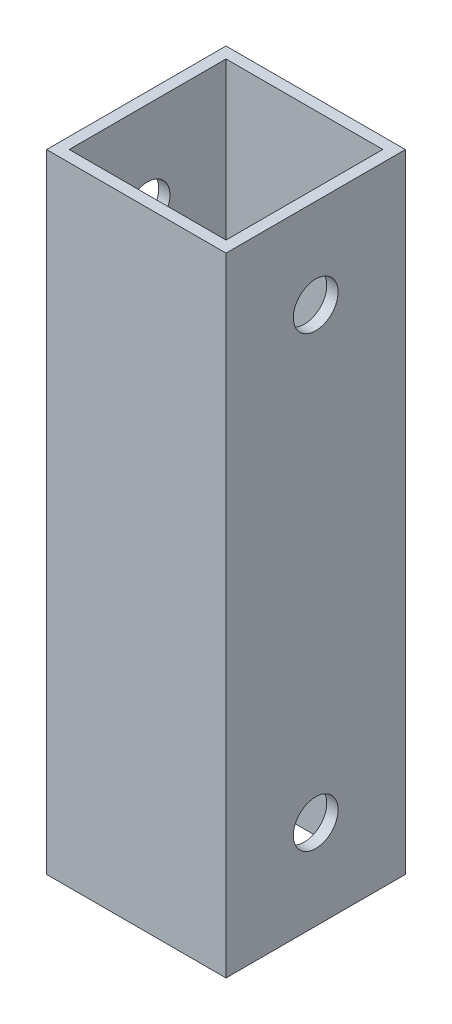
SolidWorks part; units mm, degrees
material "6061 Alloy"
ref_plane "Front Plane" through (0, 0, 0) normal (0, 0, 1) x (1, 0, 0)
ref_plane "Top Plane" through (0, 0, 0) normal (0, 1, 0) x (1, 0, 0)
ref_plane "Right Plane" through (0, 0, 0) normal (1, 0, 0) x (0, 0, -1)
sketch "Sketch1" plane through (0, 0, 0) normal (0, 1, 0) x (1, 0, 0)
  line L0 (-25.4, -25.4) -> (25.4, 25.4) construction
  line L1 (-25.4, 25.4) -> (25.4, 25.4)
  line L2 (-25.4, 25.4) -> (-25.4, -25.4)
  line L3 (-25.4, -25.4) -> (25.4, -25.4)
  line L4 (25.4, 25.4) -> (25.4, -25.4)
  line L5 (22.225, -22.225) -> (-22.225, 22.225) construction
  line L6 (-22.225, 22.225) -> (22.1918, 22.225)
  line L7 (-22.225, 22.225) -> (-22.225, -22.1918)
  line L8 (-22.225, -22.1918) -> (22.1918, -22.1918)
  line L9 (22.1918, 22.225) -> (22.1918, -22.1918)
  point P7 (0, 0)
  point P10 (0, 0)
  point P14 (0, 0)
  dimension "D1" = 50.8
  dimension "D2" = 3.175
  dimension "D3" = 3.175
extrude "Boss-Extrude1" add sketch "Sketch1" along normal blind 177.8
sketch "Sketch2" plane through (-25.4, 0, 0) normal (-1, 0, 0) x (0, 0, 1)
  line L0 (25.4, 88.9) -> (-25.4, 88.9) construction
  line L1 (25.4, 177.8) -> (25.4, 0) construction
  line L2 (-25.4, 177.8) -> (-25.4, 0) construction
  line L4 (0, 152.4) -> (0, 25.4) construction
  circle A1 centre (0, 25.4) radius 6.35
  circle A2 centre (0, 152.4) radius 6.35
  point P10 (0, 88.9)
  point P13 (0, 88.9)
  dimension "D2" = 12.7
extrude "Cut-Extrude1" cut sketch "Sketch2" against normal through all
equation "\"D1@Boss-Extrude1\"=\"HoleDist\"+2"
